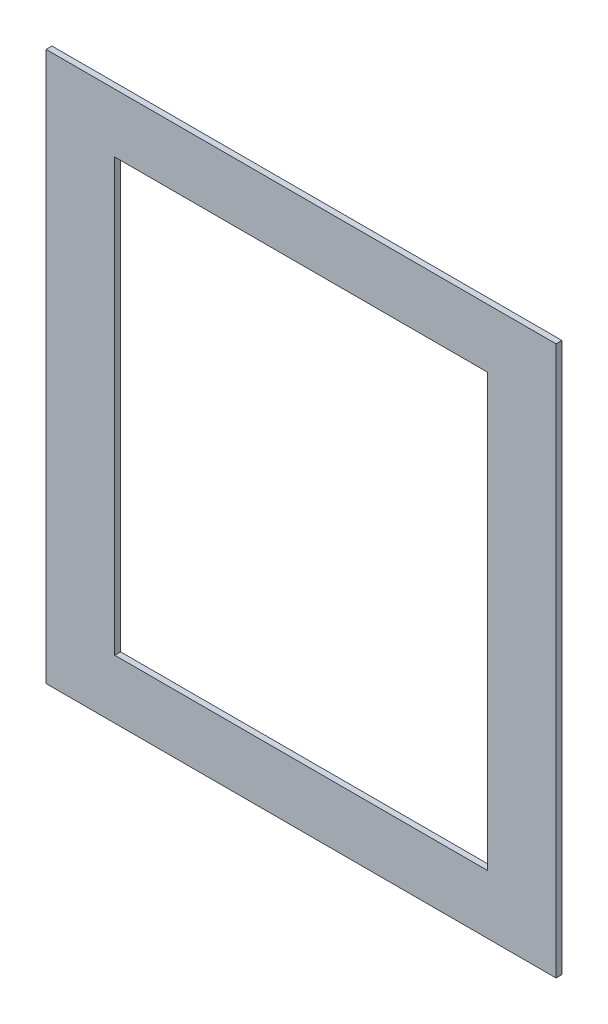
SolidWorks part; units mm, degrees
material "Клен"
ref_plane "Спереди" through (0, 0, 0) normal (0, 0, 1) x (1, 0, 0)
ref_plane "Сверху" through (0, 0, 0) normal (0, 1, 0) x (1, 0, 0)
ref_plane "Справа" through (0, 0, 0) normal (1, 0, 0) x (0, 0, -1)
sketch "Эскиз1" plane through (0, 0, 0) normal (0, 0, 1) x (1, 0, 0)
  line L0 (12.3279, 480.4642) -> (12.3279, 40.4642)
  line L1 (-57.6721, 540.4642) -> (462.3279, 540.4642)
  line L2 (-57.6721, 540.4642) -> (-57.6721, -19.5358)
  line L3 (-57.6721, -19.5358) -> (462.3279, -19.5358)
  line L4 (462.3279, 540.4642) -> (462.3279, -19.5358)
  line L5 (12.3279, 40.4642) -> (392.3279, 40.4642)
  line L6 (392.3279, 480.4642) -> (392.3279, 40.4642)
  line L7 (12.3279, 480.4642) -> (392.3279, 480.4642)
  dimension "D1" = 60
  dimension "D2" = 500
  dimension "D3" = 60
  dimension "D4" = 380
  dimension "D5" = 70
  dimension "D6" = 70
extrude "Бобышка-Вытянуть1" add sketch "Эскиз1" along normal blind 6
equation "\"sheet_thickness\"= 6"
equation "\"D1@Бобышка-Вытянуть1\"= \"sheet_thickness\""
equation "\"bottom_line\"= 60"
equation "\"width_space\"= 500"
equation "\"D6@Эскиз1\"=\"D5@Эскиз1\""
